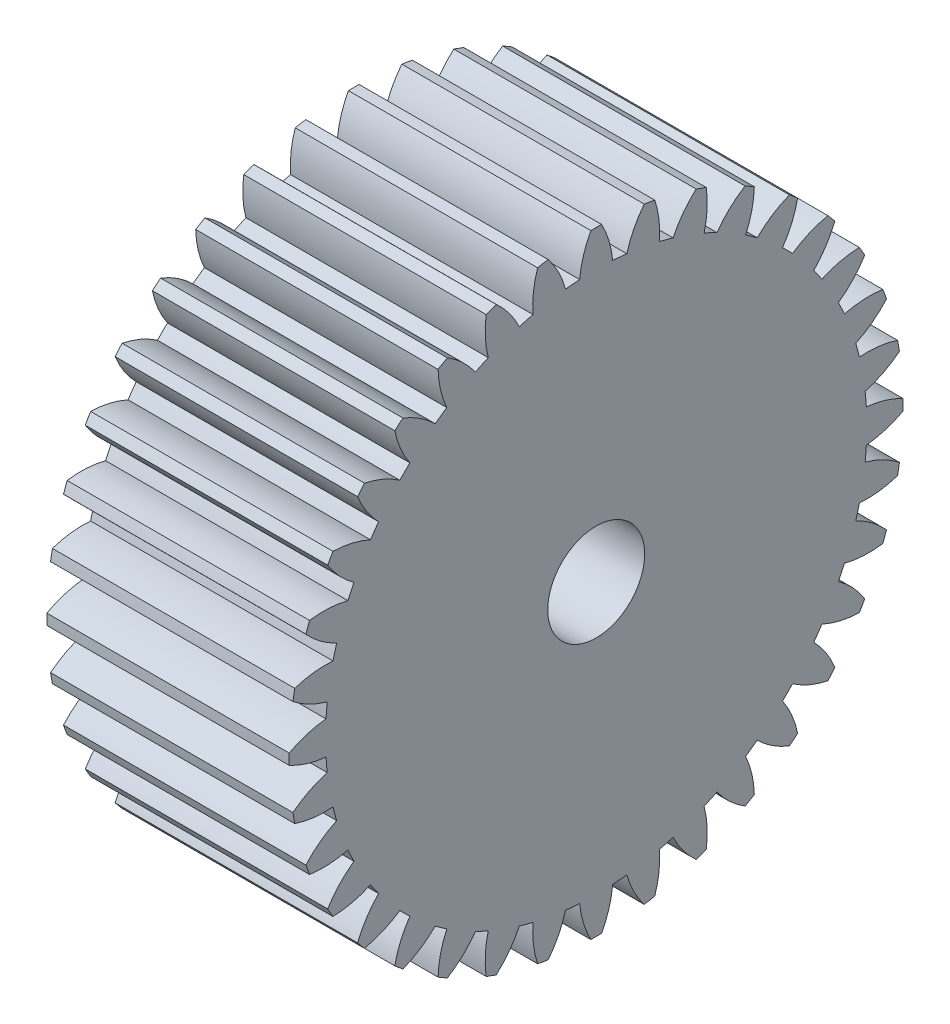
SolidWorks part; units mm, degrees
ref_plane "Front Plane" through (0, 0, 0) normal (0, 0, 1) x (1, 0, 0)
ref_plane "Top Plane" through (0, 0, 0) normal (0, 1, 0) x (1, 0, 0)
ref_plane "Right Plane" through (0, 0, 0) normal (1, 0, 0) x (0, 0, -1)
sketch "Sketch1" plane through (0, 0, 0) normal (0, 0, 1) x (1, 0, 0)
  line L0 (-9, 19) -> (-9, 0)
  line L1 (-9, 0) -> (6, 0)
  line L2 (6, 0) -> (6, 19)
  line L3 (6, 19) -> (-9, 19)
  line L4 (-9, 0) -> (6, 0) construction
  dimension "D1" = 15
  dimension "D2" = 19
revolve "Revolve1" add sketch "Sketch1" angle 360 about L4
sketch "Sketch2" plane through (-9, 0, 0) normal (-1, 0, 0) x (0, 0, 1)
  arc A0 (18.7661, -2.9723) -> (18.9971, -0.3316) centre (0, 0) ccw
  arc A1 (18.9971, -0.3316) -> (16.7188, -1.0226) centre (16.1512, 4.9505) cw
  arc A2 (16.7188, -1.0226) -> (16.6423, -1.8962) centre (0, 0) cw
  arc A3 (16.6423, -1.8962) -> (18.7661, -2.9723) centre (15.0462, -7.68) cw
extrude "Cut-Extrude1" cut sketch "Sketch2" against normal through all
sketch "Sketch3" plane through (-9, 0, 0) normal (-1, 0, 0) x (0, 0, 1)
  arc A0 (17.9649, -6.1858) -> (18.6509, -3.6254) centre (0, 0) ccw
  arc A1 (18.6509, -3.6254) -> (16.2872, -3.9102) centre (16.7655, 2.0707) cw
  arc A2 (16.2872, -3.9102) -> (16.0602, -4.7573) centre (0, 0) cw
  arc A3 (16.0602, -4.7573) -> (17.9649, -6.1858) centre (13.484, -10.176) cw
extrude "Cut-Extrude2" cut sketch "Sketch3" against normal through all
sketch "Sketch4" plane through (-9, 0, 0) normal (-1, 0, 0) x (0, 0, 1)
  arc A0 (16.6178, -9.2114) -> (17.738, -6.809) centre (0, 0) ccw
  arc A1 (17.738, -6.809) -> (15.3608, -6.679) centre (16.8704, -0.8721) cw
  arc A2 (15.3608, -6.679) -> (14.9902, -7.4738) centre (0, 0) cw
  arc A3 (14.9902, -7.4738) -> (16.6178, -9.2114) centre (11.5121, -12.3629) cw
extrude "Cut-Extrude3" cut sketch "Sketch4" against normal through all
sketch "Sketch5" plane through (-9, 0, 0) normal (-1, 0, 0) x (0, 0, 1)
  arc A0 (14.7658, -11.9571) -> (16.2862, -9.7857) centre (0, 0) ccw
  arc A1 (16.2862, -9.7857) -> (13.9676, -9.2449) centre (16.4626, -3.7883) cw
  arc A2 (13.9676, -9.2449) -> (13.4646, -9.9633) centre (0, 0) cw
  arc A3 (13.4646, -9.9633) -> (14.7658, -11.9571) centre (9.1904, -14.1741) cw
extrude "Cut-Extrude4" cut sketch "Sketch5" against normal through all
sketch "Sketch6" plane through (-9, 0, 0) normal (-1, 0, 0) x (0, 0, 1)
  arc A0 (12.4651, -14.3395) -> (14.3395, -12.4651) centre (0, 0) ccw
  arc A1 (14.3395, -12.4651) -> (12.15, -11.5299) centre (15.5547, -6.5895) cw
  arc A2 (12.15, -11.5299) -> (11.5299, -12.15) centre (0, 0) cw
  arc A3 (11.5299, -12.15) -> (12.4651, -14.3395) centre (6.5895, -15.5547) cw
extrude "Cut-Extrude5" cut sketch "Sketch6" against normal through all
sketch "Sketch7" plane through (-9, 0, 0) normal (-1, 0, 0) x (0, 0, 1)
  arc A0 (9.7857, -16.2862) -> (11.9571, -14.7658) centre (0, 0) ccw
  arc A1 (11.9571, -14.7658) -> (9.9633, -13.4646) centre (14.1741, -9.1904) cw
  arc A2 (9.9633, -13.4646) -> (9.2449, -13.9676) centre (0, 0) cw
  arc A3 (9.2449, -13.9676) -> (9.7857, -16.2862) centre (3.7883, -16.4626) cw
extrude "Cut-Extrude6" cut sketch "Sketch7" against normal through all
sketch "Sketch8" plane through (-9, 0, 0) normal (-1, 0, 0) x (0, 0, 1)
  arc A0 (6.809, -17.738) -> (9.2114, -16.6178) centre (0, 0) ccw
  arc A1 (9.2114, -16.6178) -> (7.4738, -14.9902) centre (12.3629, -11.5121) cw
  arc A2 (7.4738, -14.9902) -> (6.679, -15.3608) centre (0, 0) cw
  arc A3 (6.679, -15.3608) -> (6.809, -17.738) centre (0.8721, -16.8704) cw
extrude "Cut-Extrude7" cut sketch "Sketch8" against normal through all
sketch "Sketch9" plane through (-9, 0, 0) normal (-1, 0, 0) x (0, 0, 1)
  arc A0 (3.6254, -18.6509) -> (6.1858, -17.9649) centre (0, 0) ccw
  arc A1 (6.1858, -17.9649) -> (4.7573, -16.0602) centre (10.176, -13.484) cw
  arc A2 (4.7573, -16.0602) -> (3.9102, -16.2872) centre (0, 0) cw
  arc A3 (3.9102, -16.2872) -> (3.6254, -18.6509) centre (-2.0707, -16.7655) cw
extrude "Cut-Extrude8" cut sketch "Sketch9" against normal through all
sketch "Sketch10" plane through (-9, 0, 0) normal (-1, 0, 0) x (0, 0, 1)
  arc A0 (0.3316, -18.9971) -> (2.9723, -18.7661) centre (0, 0) ccw
  arc A1 (2.9723, -18.7661) -> (1.8962, -16.6423) centre (7.68, -15.0462) cw
  arc A2 (1.8962, -16.6423) -> (1.0226, -16.7188) centre (0, 0) cw
  arc A3 (1.0226, -16.7188) -> (0.3316, -18.9971) centre (-4.9505, -16.1512) cw
extrude "Cut-Extrude9" cut sketch "Sketch10" against normal through all
sketch "Sketch11" plane through (-9, 0, 0) normal (-1, 0, 0) x (0, 0, 1)
  arc A0 (-2.9723, -18.7661) -> (-0.3316, -18.9971) centre (0, 0) ccw
  arc A1 (-0.3316, -18.9971) -> (-1.0226, -16.7188) centre (4.9505, -16.1512) cw
  arc A2 (-1.0226, -16.7188) -> (-1.8962, -16.6423) centre (0, 0) cw
  arc A3 (-1.8962, -16.6423) -> (-2.9723, -18.7661) centre (-7.68, -15.0462) cw
extrude "Cut-Extrude10" cut sketch "Sketch11" against normal through all
sketch "Sketch12" plane through (-9, 0, 0) normal (-1, 0, 0) x (0, 0, 1)
  arc A0 (-6.1858, -17.9649) -> (-3.6254, -18.6509) centre (0, 0) ccw
  arc A1 (-3.6254, -18.6509) -> (-3.9102, -16.2872) centre (2.0707, -16.7655) cw
  arc A2 (-3.9102, -16.2872) -> (-4.7573, -16.0602) centre (0, 0) cw
  arc A3 (-4.7573, -16.0602) -> (-6.1858, -17.9649) centre (-10.176, -13.484) cw
extrude "Cut-Extrude11" cut sketch "Sketch12" against normal through all
sketch "Sketch13" plane through (-9, 0, 0) normal (-1, 0, 0) x (0, 0, 1)
  arc A0 (-9.2114, -16.6178) -> (-6.809, -17.738) centre (0, 0) ccw
  arc A1 (-6.809, -17.738) -> (-6.679, -15.3608) centre (-0.8721, -16.8704) cw
  arc A2 (-6.679, -15.3608) -> (-7.4738, -14.9902) centre (0, 0) cw
  arc A3 (-7.4738, -14.9902) -> (-9.2114, -16.6178) centre (-12.3629, -11.5121) cw
extrude "Cut-Extrude12" cut sketch "Sketch13" against normal through all
sketch "Sketch14" plane through (-9, 0, 0) normal (-1, 0, 0) x (0, 0, 1)
  arc A0 (-11.9571, -14.7658) -> (-9.7857, -16.2862) centre (0, 0) ccw
  arc A1 (-9.7857, -16.2862) -> (-9.2449, -13.9676) centre (-3.7883, -16.4626) cw
  arc A2 (-9.2449, -13.9676) -> (-9.9633, -13.4646) centre (0, 0) cw
  arc A3 (-9.9633, -13.4646) -> (-11.9571, -14.7658) centre (-14.1741, -9.1904) cw
extrude "Cut-Extrude13" cut sketch "Sketch14" against normal through all
sketch "Sketch15" plane through (-9, 0, 0) normal (-1, 0, 0) x (0, 0, 1)
  arc A0 (-14.3395, -12.4651) -> (-12.4651, -14.3395) centre (0, 0) ccw
  arc A1 (-12.4651, -14.3395) -> (-11.5299, -12.15) centre (-6.5895, -15.5547) cw
  arc A2 (-11.5299, -12.15) -> (-12.15, -11.5299) centre (0, 0) cw
  arc A3 (-12.15, -11.5299) -> (-14.3395, -12.4651) centre (-15.5547, -6.5895) cw
extrude "Cut-Extrude14" cut sketch "Sketch15" against normal through all
sketch "Sketch16" plane through (-9, 0, 0) normal (-1, 0, 0) x (0, 0, 1)
  arc A0 (-16.2862, -9.7857) -> (-14.7658, -11.9571) centre (0, 0) ccw
  arc A1 (-14.7658, -11.9571) -> (-13.4646, -9.9633) centre (-9.1904, -14.1741) cw
  arc A2 (-13.4646, -9.9633) -> (-13.9676, -9.2449) centre (0, 0) cw
  arc A3 (-13.9676, -9.2449) -> (-16.2862, -9.7857) centre (-16.4626, -3.7883) cw
extrude "Cut-Extrude15" cut sketch "Sketch16" against normal through all
sketch "Sketch17" plane through (-9, 0, 0) normal (-1, 0, 0) x (0, 0, 1)
  arc A0 (-17.738, -6.809) -> (-16.6178, -9.2114) centre (0, 0) ccw
  arc A1 (-16.6178, -9.2114) -> (-14.9902, -7.4738) centre (-11.5121, -12.3629) cw
  arc A2 (-14.9902, -7.4738) -> (-15.3608, -6.679) centre (0, 0) cw
  arc A3 (-15.3608, -6.679) -> (-17.738, -6.809) centre (-16.8704, -0.8721) cw
extrude "Cut-Extrude16" cut sketch "Sketch17" against normal through all
sketch "Sketch18" plane through (-9, 0, 0) normal (-1, 0, 0) x (0, 0, 1)
  arc A0 (-18.6509, -3.6254) -> (-17.9649, -6.1858) centre (0, 0) ccw
  arc A1 (-17.9649, -6.1858) -> (-16.0602, -4.7573) centre (-13.484, -10.176) cw
  arc A2 (-16.0602, -4.7573) -> (-16.2872, -3.9102) centre (0, 0) cw
  arc A3 (-16.2872, -3.9102) -> (-18.6509, -3.6254) centre (-16.7655, 2.0707) cw
extrude "Cut-Extrude17" cut sketch "Sketch18" against normal through all
sketch "Sketch19" plane through (-9, 0, 0) normal (-1, 0, 0) x (0, 0, 1)
  arc A0 (-18.9971, -0.3316) -> (-18.7661, -2.9723) centre (0, 0) ccw
  arc A1 (-18.7661, -2.9723) -> (-16.6423, -1.8962) centre (-15.0462, -7.68) cw
  arc A2 (-16.6423, -1.8962) -> (-16.7188, -1.0226) centre (0, 0) cw
  arc A3 (-16.7188, -1.0226) -> (-18.9971, -0.3316) centre (-16.1512, 4.9505) cw
extrude "Cut-Extrude18" cut sketch "Sketch19" against normal through all
sketch "Sketch20" plane through (-9, 0, 0) normal (-1, 0, 0) x (0, 0, 1)
  arc A0 (-18.7661, 2.9723) -> (-18.9971, 0.3316) centre (0, 0) ccw
  arc A1 (-18.9971, 0.3316) -> (-16.7188, 1.0226) centre (-16.1512, -4.9505) cw
  arc A2 (-16.7188, 1.0226) -> (-16.6423, 1.8962) centre (0, 0) cw
  arc A3 (-16.6423, 1.8962) -> (-18.7661, 2.9723) centre (-15.0462, 7.68) cw
extrude "Cut-Extrude19" cut sketch "Sketch20" against normal through all
sketch "Sketch21" plane through (-9, 0, 0) normal (-1, 0, 0) x (0, 0, 1)
  arc A0 (-17.9649, 6.1858) -> (-18.6509, 3.6254) centre (0, 0) ccw
  arc A1 (-18.6509, 3.6254) -> (-16.2872, 3.9102) centre (-16.7655, -2.0707) cw
  arc A2 (-16.2872, 3.9102) -> (-16.0602, 4.7573) centre (0, 0) cw
  arc A3 (-16.0602, 4.7573) -> (-17.9649, 6.1858) centre (-13.484, 10.176) cw
extrude "Cut-Extrude20" cut sketch "Sketch21" against normal through all
sketch "Sketch22" plane through (-9, 0, 0) normal (-1, 0, 0) x (0, 0, 1)
  arc A0 (-16.6178, 9.2114) -> (-17.738, 6.809) centre (0, 0) ccw
  arc A1 (-17.738, 6.809) -> (-15.3608, 6.679) centre (-16.8704, 0.8721) cw
  arc A2 (-15.3608, 6.679) -> (-14.9902, 7.4738) centre (0, 0) cw
  arc A3 (-14.9902, 7.4738) -> (-16.6178, 9.2114) centre (-11.5121, 12.3629) cw
extrude "Cut-Extrude21" cut sketch "Sketch22" against normal through all
sketch "Sketch23" plane through (-9, 0, 0) normal (-1, 0, 0) x (0, 0, 1)
  arc A0 (-14.7658, 11.9571) -> (-16.2862, 9.7857) centre (0, 0) ccw
  arc A1 (-16.2862, 9.7857) -> (-13.9676, 9.2449) centre (-16.4626, 3.7883) cw
  arc A2 (-13.9676, 9.2449) -> (-13.4646, 9.9633) centre (0, 0) cw
  arc A3 (-13.4646, 9.9633) -> (-14.7658, 11.9571) centre (-9.1904, 14.1741) cw
extrude "Cut-Extrude22" cut sketch "Sketch23" against normal through all
sketch "Sketch24" plane through (-9, 0, 0) normal (-1, 0, 0) x (0, 0, 1)
  arc A0 (-12.4651, 14.3395) -> (-14.3395, 12.4651) centre (0, 0) ccw
  arc A1 (-14.3395, 12.4651) -> (-12.15, 11.5299) centre (-15.5547, 6.5895) cw
  arc A2 (-12.15, 11.5299) -> (-11.5299, 12.15) centre (0, 0) cw
  arc A3 (-11.5299, 12.15) -> (-12.4651, 14.3395) centre (-6.5895, 15.5547) cw
extrude "Cut-Extrude23" cut sketch "Sketch24" against normal through all
sketch "Sketch25" plane through (-9, 0, 0) normal (-1, 0, 0) x (0, 0, 1)
  arc A0 (-9.7857, 16.2862) -> (-11.9571, 14.7658) centre (0, 0) ccw
  arc A1 (-11.9571, 14.7658) -> (-9.9633, 13.4646) centre (-14.1741, 9.1904) cw
  arc A2 (-9.9633, 13.4646) -> (-9.2449, 13.9676) centre (0, 0) cw
  arc A3 (-9.2449, 13.9676) -> (-9.7857, 16.2862) centre (-3.7883, 16.4626) cw
extrude "Cut-Extrude24" cut sketch "Sketch25" against normal through all
sketch "Sketch26" plane through (-9, 0, 0) normal (-1, 0, 0) x (0, 0, 1)
  arc A0 (-6.809, 17.738) -> (-9.2114, 16.6178) centre (0, 0) ccw
  arc A1 (-9.2114, 16.6178) -> (-7.4738, 14.9902) centre (-12.3629, 11.5121) cw
  arc A2 (-7.4738, 14.9902) -> (-6.679, 15.3608) centre (0, 0) cw
  arc A3 (-6.679, 15.3608) -> (-6.809, 17.738) centre (-0.8721, 16.8704) cw
extrude "Cut-Extrude25" cut sketch "Sketch26" against normal through all
sketch "Sketch27" plane through (-9, 0, 0) normal (-1, 0, 0) x (0, 0, 1)
  arc A0 (-3.6254, 18.6509) -> (-6.1858, 17.9649) centre (0, 0) ccw
  arc A1 (-6.1858, 17.9649) -> (-4.7573, 16.0602) centre (-10.176, 13.484) cw
  arc A2 (-4.7573, 16.0602) -> (-3.9102, 16.2872) centre (0, 0) cw
  arc A3 (-3.9102, 16.2872) -> (-3.6254, 18.6509) centre (2.0707, 16.7655) cw
extrude "Cut-Extrude26" cut sketch "Sketch27" against normal through all
sketch "Sketch28" plane through (-9, 0, 0) normal (-1, 0, 0) x (0, 0, 1)
  arc A0 (-0.3316, 18.9971) -> (-2.9723, 18.7661) centre (0, 0) ccw
  arc A1 (-2.9723, 18.7661) -> (-1.8962, 16.6423) centre (-7.68, 15.0462) cw
  arc A2 (-1.8962, 16.6423) -> (-1.0226, 16.7188) centre (0, 0) cw
  arc A3 (-1.0226, 16.7188) -> (-0.3316, 18.9971) centre (4.9505, 16.1512) cw
extrude "Cut-Extrude27" cut sketch "Sketch28" against normal through all
sketch "Sketch29" plane through (-9, 0, 0) normal (-1, 0, 0) x (0, 0, 1)
  arc A0 (2.9723, 18.7661) -> (0.3316, 18.9971) centre (0, 0) ccw
  arc A1 (0.3316, 18.9971) -> (1.0226, 16.7188) centre (-4.9505, 16.1512) cw
  arc A2 (1.0226, 16.7188) -> (1.8962, 16.6423) centre (0, 0) cw
  arc A3 (1.8962, 16.6423) -> (2.9723, 18.7661) centre (7.68, 15.0462) cw
extrude "Cut-Extrude28" cut sketch "Sketch29" against normal through all
sketch "Sketch30" plane through (-9, 0, 0) normal (-1, 0, 0) x (0, 0, 1)
  arc A0 (6.1858, 17.9649) -> (3.6254, 18.6509) centre (0, 0) ccw
  arc A1 (3.6254, 18.6509) -> (3.9102, 16.2872) centre (-2.0707, 16.7655) cw
  arc A2 (3.9102, 16.2872) -> (4.7573, 16.0602) centre (0, 0) cw
  arc A3 (4.7573, 16.0602) -> (6.1858, 17.9649) centre (10.176, 13.484) cw
extrude "Cut-Extrude29" cut sketch "Sketch30" against normal through all
sketch "Sketch31" plane through (-9, 0, 0) normal (-1, 0, 0) x (0, 0, 1)
  arc A0 (9.2114, 16.6178) -> (6.809, 17.738) centre (0, 0) ccw
  arc A1 (6.809, 17.738) -> (6.679, 15.3608) centre (0.8721, 16.8704) cw
  arc A2 (6.679, 15.3608) -> (7.4738, 14.9902) centre (0, 0) cw
  arc A3 (7.4738, 14.9902) -> (9.2114, 16.6178) centre (12.3629, 11.5121) cw
extrude "Cut-Extrude30" cut sketch "Sketch31" against normal through all
sketch "Sketch32" plane through (-9, 0, 0) normal (-1, 0, 0) x (0, 0, 1)
  arc A0 (11.9571, 14.7658) -> (9.7857, 16.2862) centre (0, 0) ccw
  arc A1 (9.7857, 16.2862) -> (9.2449, 13.9676) centre (3.7883, 16.4626) cw
  arc A2 (9.2449, 13.9676) -> (9.9633, 13.4646) centre (0, 0) cw
  arc A3 (9.9633, 13.4646) -> (11.9571, 14.7658) centre (14.1741, 9.1904) cw
extrude "Cut-Extrude31" cut sketch "Sketch32" against normal through all
sketch "Sketch33" plane through (-9, 0, 0) normal (-1, 0, 0) x (0, 0, 1)
  arc A0 (14.3395, 12.4651) -> (12.4651, 14.3395) centre (0, 0) ccw
  arc A1 (12.4651, 14.3395) -> (11.5299, 12.15) centre (6.5895, 15.5547) cw
  arc A2 (11.5299, 12.15) -> (12.15, 11.5299) centre (0, 0) cw
  arc A3 (12.15, 11.5299) -> (14.3395, 12.4651) centre (15.5547, 6.5895) cw
extrude "Cut-Extrude32" cut sketch "Sketch33" against normal through all
sketch "Sketch34" plane through (-9, 0, 0) normal (-1, 0, 0) x (0, 0, 1)
  arc A0 (16.2862, 9.7857) -> (14.7658, 11.9571) centre (0, 0) ccw
  arc A1 (14.7658, 11.9571) -> (13.4646, 9.9633) centre (9.1904, 14.1741) cw
  arc A2 (13.4646, 9.9633) -> (13.9676, 9.2449) centre (0, 0) cw
  arc A3 (13.9676, 9.2449) -> (16.2862, 9.7857) centre (16.4626, 3.7883) cw
extrude "Cut-Extrude33" cut sketch "Sketch34" against normal through all
sketch "Sketch35" plane through (-9, 0, 0) normal (-1, 0, 0) x (0, 0, 1)
  arc A0 (17.738, 6.809) -> (16.6178, 9.2114) centre (0, 0) ccw
  arc A1 (16.6178, 9.2114) -> (14.9902, 7.4738) centre (11.5121, 12.3629) cw
  arc A2 (14.9902, 7.4738) -> (15.3608, 6.679) centre (0, 0) cw
  arc A3 (15.3608, 6.679) -> (17.738, 6.809) centre (16.8704, 0.8721) cw
extrude "Cut-Extrude34" cut sketch "Sketch35" against normal through all
sketch "Sketch36" plane through (-9, 0, 0) normal (-1, 0, 0) x (0, 0, 1)
  arc A0 (18.6509, 3.6254) -> (17.9649, 6.1858) centre (0, 0) ccw
  arc A1 (17.9649, 6.1858) -> (16.0602, 4.7573) centre (13.484, 10.176) cw
  arc A2 (16.0602, 4.7573) -> (16.2872, 3.9102) centre (0, 0) cw
  arc A3 (16.2872, 3.9102) -> (18.6509, 3.6254) centre (16.7655, -2.0707) cw
extrude "Cut-Extrude35" cut sketch "Sketch36" against normal through all
sketch "Sketch37" plane through (-9, 0, 0) normal (-1, 0, 0) x (0, 0, 1)
  arc A0 (18.9971, 0.3316) -> (18.7661, 2.9723) centre (0, 0) ccw
  arc A1 (18.7661, 2.9723) -> (16.6423, 1.8962) centre (15.0462, 7.68) cw
  arc A2 (16.6423, 1.8962) -> (16.7188, 1.0226) centre (0, 0) cw
  arc A3 (16.7188, 1.0226) -> (18.9971, 0.3316) centre (16.1512, -4.9505) cw
extrude "Cut-Extrude36" cut sketch "Sketch37" against normal through all
sketch "Sketch46" plane through (6, 0, 0) normal (1, 0, 0) x (0, 0, -1)
  circle A0 centre (0, 0) radius 3
  dimension "D1" = 6
extrude "Cut-Extrude37" cut sketch "Sketch46" against normal through all
